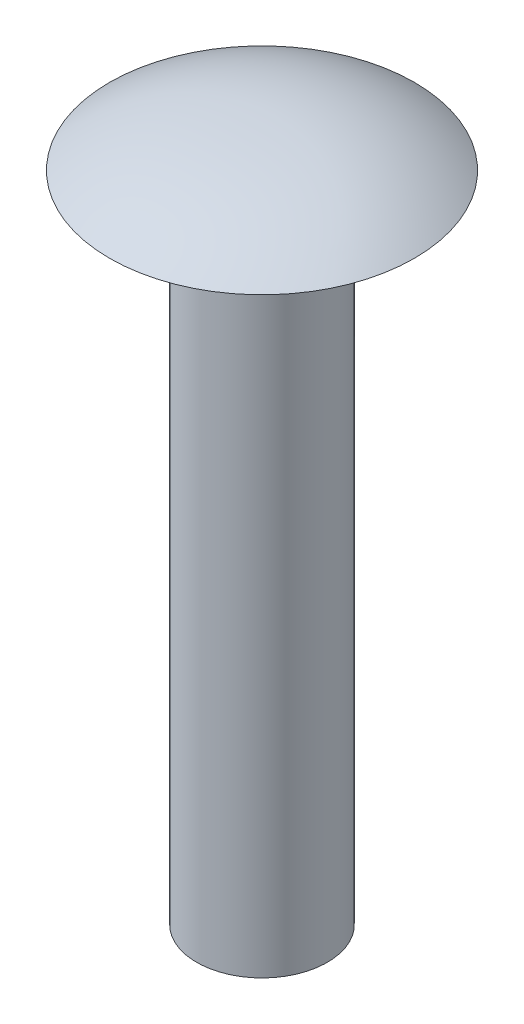
SolidWorks part; units mm, degrees
ref_plane "Front Plane" through (0, 0, 0) normal (0, 0, 1) x (1, 0, 0)
ref_plane "Top Plane" through (0, 0, 0) normal (0, 1, 0) x (1, 0, 0)
ref_plane "Right Plane" through (0, 0, 0) normal (1, 0, 0) x (0, 0, -1)
sketch "Szkic1" plane through (0, 0, 0) normal (0, 0, 1) x (1, 0, 0)
  line L0 (0, 0) -> (0, 32)
  line L1 (0, 0) -> (3, 0)
  line L2 (3, 0) -> (3, 30)
  line L3 (3, 30) -> (7, 30)
  line L4 (0.8462, 32) -> (-0.8462, 32) construction
  line L5 (16.07, 23.6491) -> (-2.07, 36.3509) construction
  spline S0 degree 3 poles (0, 32) (2.6667, 32) (4.8156, 31.5295) (7, 30) knots 0 0 0 0 1 1 1 1
  dimension "D5" = 8
  dimension "D6" = 35
  dimension "D7" = 8
  dimension "D1" = 2
  dimension "D2" = 4
  dimension "D3" = 3
  dimension "D4" = 32
revolve "Obrót1" add sketch "Szkic1" angle 360 about L0
